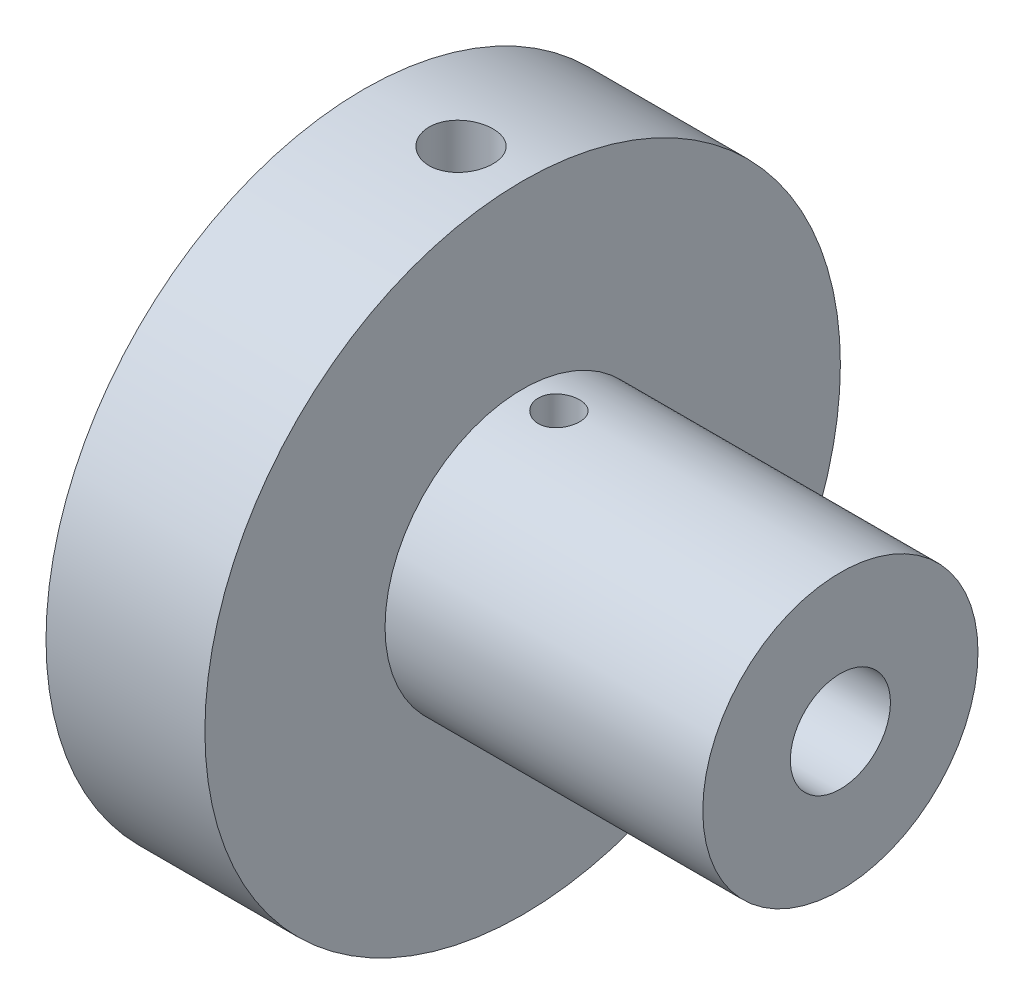
SolidWorks part; units mm, degrees
ref_plane "Front Plane" through (0, 0, 0) normal (0, 0, 1) x (1, 0, 0)
ref_plane "Top Plane" through (0, 0, 0) normal (0, 1, 0) x (1, 0, 0)
ref_plane "Right Plane" through (0, 0, 0) normal (1, 0, 0) x (0, 0, -1)
sketch "Sketch2" plane through (0, 0, 0) normal (1, 0, 0) x (0, 0, -1)
  circle A0 centre (0, 0) radius 11
  dimension "D1" = 22
ref_plane "Plane1" through (0, 25.2, 0) normal (0, 1, 0) x (1, 0, 0)
extrude "Boss-Extrude2" add sketch "Sketch2" along normal blind 25.4
sketch "Sketch7" plane through (25.4, 0, 0) normal (1, 0, 0) x (0, 0, -1)
  circle A0 centre (0, 0) radius 4
  dimension "D1" = 8
extrude "Cut-Extrude3" cut sketch "Sketch7" against normal through all
sketch "Sketch8" plane through (0, 0, 0) normal (-1, 0, 0) x (0, 0, 1)
  circle A0 centre (0, 0) radius 25.4
  dimension "D1" = 50.8
extrude "Boss-Extrude3" add sketch "Sketch8" along normal blind 12.7
sketch "Sketch10" plane through (0, 0, 0) normal (1, 0, 0) x (0, 0, -1)
  circle A0 centre (0, 0) radius 4
  dimension "D1" = 8
extrude "Cut-Extrude5" cut sketch "Sketch10" against normal through all
hole_wizard "1/4-20 Tapped Hole1" positions "3DSketch2" profile "Sketch14" tap size "1/4-20" standard "ANSI Inch" end condition through all
sketch3d "3DSketch2"
  line L0 (0, 0, 0) -> (-4.9212, 0, 0) construction
  line L1 (-4.9212, 0, 0) -> (-4.9212, 33.4074, 0) construction
  line L4 (-4.9212, 33.4074, 0) -> (-4.4793, 33.4074, 0)
  point P3 (-4.9212, 25.4, 0)
sketch "Sketch14" plane through (-4.9212, 25.4, 0) normal (1, 0, 0) x (0, 0, 1)
  line L0 (0, 0) -> (0, 50.8)
  line L1 (0, 50.8) -> (2.5527, 50.8)
  line L2 (2.5527, 50.8) -> (2.5527, 0)
  line L5 (2.5527, 0) -> (0, 0)
  line L11 (0, -6.35) -> (0, 107.95) construction
  dimension "Thru Tap Drill Dia." = 5.1054
  dimension "Thru Tap Drill Depth" = 50.8
cosmetic thread "Hole Thread7" parameters "D2"=6.35
hole_wizard "M4x0.7 Tapped Hole2" positions "3DSketch4" profile "Sketch15" tap size "M4x0.7" standard "ANSI Metric"
sketch3d "3DSketch4"
  point P0 (2.9008, 11, 0)
sketch "Sketch15" plane through (2.9008, 11, 0) normal (1, 0, 0) x (0, 0, 1)
  line L0 (0, 0) -> (0, 12.1674)
  line L1 (0, 12.1674) -> (1.65, 11.176)
  line L2 (1.65, 11.176) -> (1.65, 0)
  line L5 (1.65, 0) -> (0, 0)
  line L10 (0, 12.1674) -> (-1.65, 11.176) construction
  line L11 (0, -6.35) -> (0, 107.95) construction
  dimension "Tap Drill Dia." = 3.3
  dimension "Tap Drill Depth" = 11.176
  dimension "Drill Angle" = 118
cosmetic thread "Hole Thread5" parameters "D1"=7.62, "D2"=4
